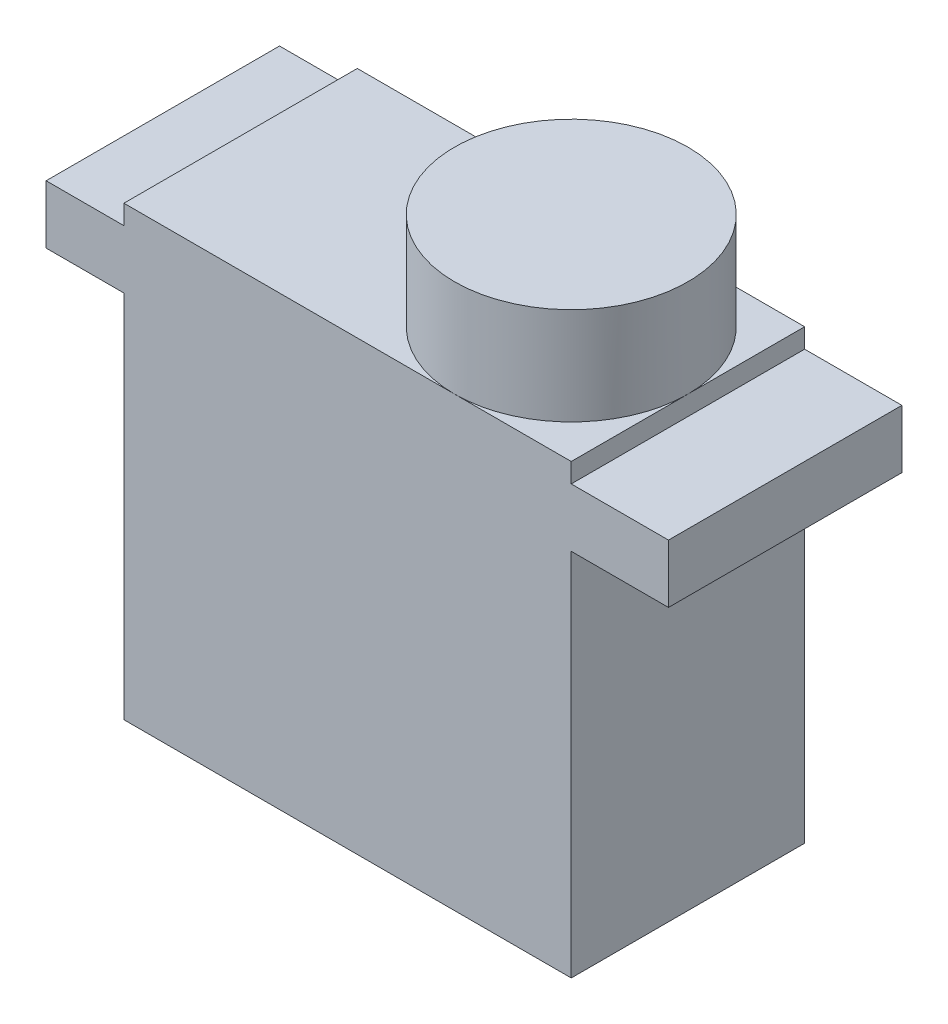
SolidWorks part; units mm, degrees
ref_plane "Plan de face" through (0, 0, 0) normal (0, 0, 1) x (1, 0, 0)
ref_plane "Plan de dessus" through (0, 0, 0) normal (0, 1, 0) x (1, 0, 0)
ref_plane "Plan de droite" through (0, 0, 0) normal (1, 0, 0) x (0, 0, -1)
ref_plane "hauteur corps" through (0, 19, 0) normal (0, 1, 0) x (1, 0, 0)
ref_plane "hauteur plaque vis" through (0, 22, 0) normal (0, 1, 0) x (1, 0, 0)
ref_plane "hauteur servo" through (0, 23, 0) normal (0, 1, 0) x (1, 0, 0)
ref_plane "hauteur axe" through (0, 28, 0) normal (0, 1, 0) x (1, 0, 0)
sketch "corps servo" plane through (0, 0, 0) normal (0, 1, 0) x (1, 0, 0)
  line L1 (0, 0) -> (23, 0)
  line L2 (0, 0) -> (0, 12)
  line L3 (0, 12) -> (23, 12)
  line L4 (23, 0) -> (23, 12)
  dimension "D1" = 12
  dimension "D2" = 23
extrude "Boss.-Extru.2" add sketch "corps servo" along normal up to surface (19 mm away) up to plane "hauteur corps"
sketch "plaque trous" plane through (0, 19, 0) normal (0, 1, 0) x (1, 0, 0)
  line L0 (0, 0) -> (23, 0) construction
  line L1 (-4, 0) -> (28, 0)
  line L2 (-4, 0) -> (-4, 12)
  line L3 (-4, 12) -> (28, 12)
  line L4 (28, 0) -> (28, 12)
  line L5 (23, 0) -> (23, 12) construction
  dimension "D1" = 32
  dimension "D2" = 12
  dimension "D3" = 5
extrude "Boss.-Extru.3" add sketch "plaque trous" along normal up to surface (3 mm away) up to plane "hauteur plaque vis"
sketch "Esquisse5" plane through (0, 22, 0) normal (0, 1, 0) x (1, 0, 0)
  line L0 (23, 0) -> (23, 12) construction
  line L1 (0, 0) -> (23, 0)
  line L2 (0, 0) -> (0, 12)
  line L3 (0, 12) -> (23, 12)
  line L4 (23, 0) -> (23, 12)
  line L5 (23, 12) -> (0, 12) construction
extrude "Boss.-Extru.4" add sketch "Esquisse5" along normal up to surface (1 mm away) up to plane "hauteur servo"
sketch "Esquisse6" plane through (0, 23, 0) normal (0, 1, 0) x (1, 0, 0)
  line L0 (23, 12) -> (0, 12) construction
  line L1 (23, 0) -> (23, 12) construction
  circle A0 centre (17, 6) radius 6
  dimension "D1" = 12
  dimension "D2" = 6
  dimension "D3" = 6
extrude "Boss.-Extru.5" add sketch "Esquisse6" along normal up to surface (5 mm away) up to plane "hauteur axe"
